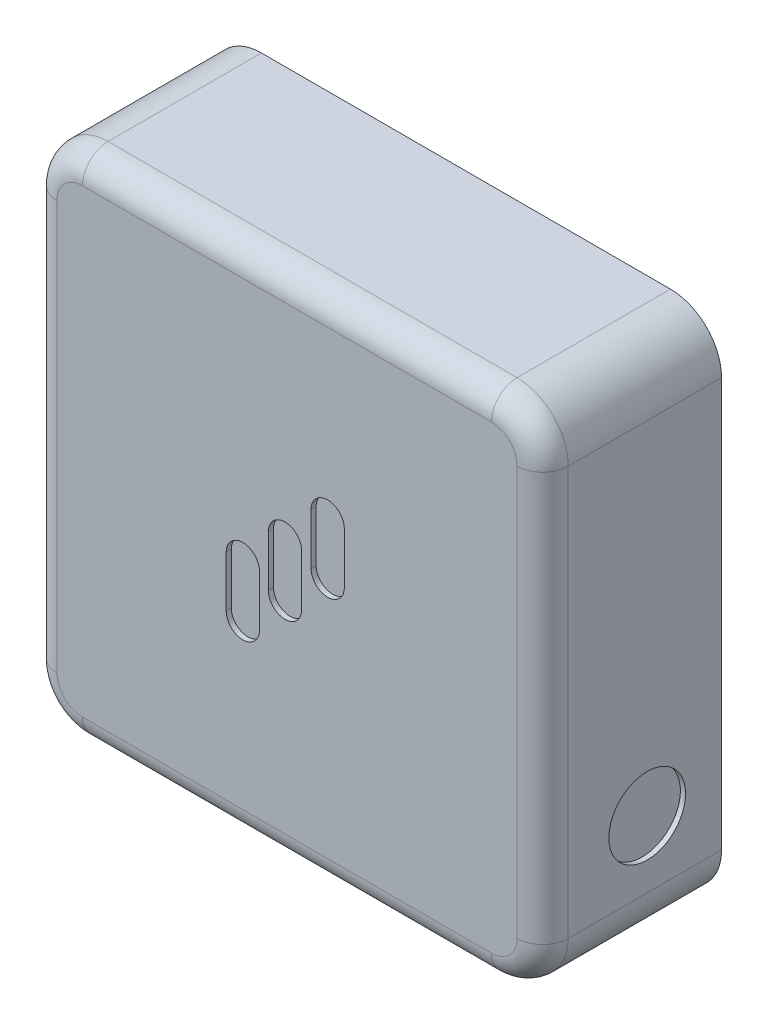
SolidWorks part; units mm, degrees
ref_plane "Front Plane" through (0, 0, 0) normal (0, 0, 1) x (1, 0, 0)
ref_plane "Top Plane" through (0, 0, 0) normal (0, 1, 0) x (1, 0, 0)
ref_plane "Right Plane" through (0, 0, 0) normal (1, 0, 0) x (0, 0, -1)
sketch "Sketch1" plane through (0, 0, 0) normal (0, 0, 1) x (1, 0, 0)
  line L1 (-57.3786, 26.1554) -> (42.6214, 26.1554)
  line L2 (-57.3786, 26.1554) -> (-57.3786, -73.8446)
  line L3 (-57.3786, -73.8446) -> (42.6214, -73.8446)
  line L4 (42.6214, 26.1554) -> (42.6214, -73.8446)
extrude "Boss-Extrude2" add sketch "Sketch1" along normal blind 35 contours L1 L4 L3 L2
fillet "Fillet3" radius 10 4 edges at (42.6214, -73.8446, 17.5) (-57.3786, -73.8446, 17.5) (-57.3786, 26.1554, 17.5) (42.6214, 26.1554, 17.5)
fillet "Fillet4" radius 5 8 edges at (-54.4497, -70.9157, 35) (-57.3786, -23.8446, 35) (-54.4497, 23.2265, 35) (-7.3786, 26.1554, 35) (39.6925, 23.2265, 35) (42.6214, -23.8446, 35) (39.6925, -70.9157, 35) (-7.3786, -73.8446, 35)
sketch "Sketch2" plane through (42.6214, 0, 0) normal (1, 0, 0) x (0, 0, -1)
  circle A0 centre (-14.5504, -50.7845) radius 7.5
  dimension "D1" = 15
extrude "Cut-Extrude1" cut sketch "Sketch2" against normal blind 1
sketch "Sketch3" plane through (0, 0, 35) normal (0, 0, 1) x (1, 0, 0)
  line L0 (-16.0179, -36.8221) -> (-16.0179, -26.8511) construction
  line L1 (-19.2738, -36.8221) -> (-19.2738, -26.8511)
  line L2 (-12.762, -36.8221) -> (-12.762, -26.8511)
  line L3 (-7.7719, -29.2243) -> (-7.7719, -19.2534) construction
  line L4 (-11.0278, -29.2243) -> (-11.0278, -19.2534)
  line L5 (-4.516, -29.2243) -> (-4.516, -19.2534)
  line L6 (0.5741, -21.3115) -> (0.5741, -11.3406) construction
  line L7 (-2.6817, -21.3115) -> (-2.6817, -11.3406)
  line L8 (3.83, -21.3115) -> (3.83, -11.3406)
  arc A0 (-19.2738, -36.8221) -> (-12.762, -36.8221) centre (-16.0179, -36.8221) ccw
  arc A1 (-12.762, -26.8511) -> (-19.2738, -26.8511) centre (-16.0179, -26.8511) ccw
  arc A2 (-11.0278, -29.2243) -> (-4.516, -29.2243) centre (-7.7719, -29.2243) ccw
  arc A3 (-4.516, -19.2534) -> (-11.0278, -19.2534) centre (-7.7719, -19.2534) ccw
  arc A4 (-2.6817, -21.3115) -> (3.83, -21.3115) centre (0.5741, -21.3115) ccw
  arc A5 (3.83, -11.3406) -> (-2.6817, -11.3406) centre (0.5741, -11.3406) ccw
  point P2 (-16.0179, -31.8366)
  point P10 (-7.7719, -24.2388)
  point P17 (0.5741, -16.326)
extrude "Cut-Extrude2" cut sketch "Sketch3" against normal blind 1
